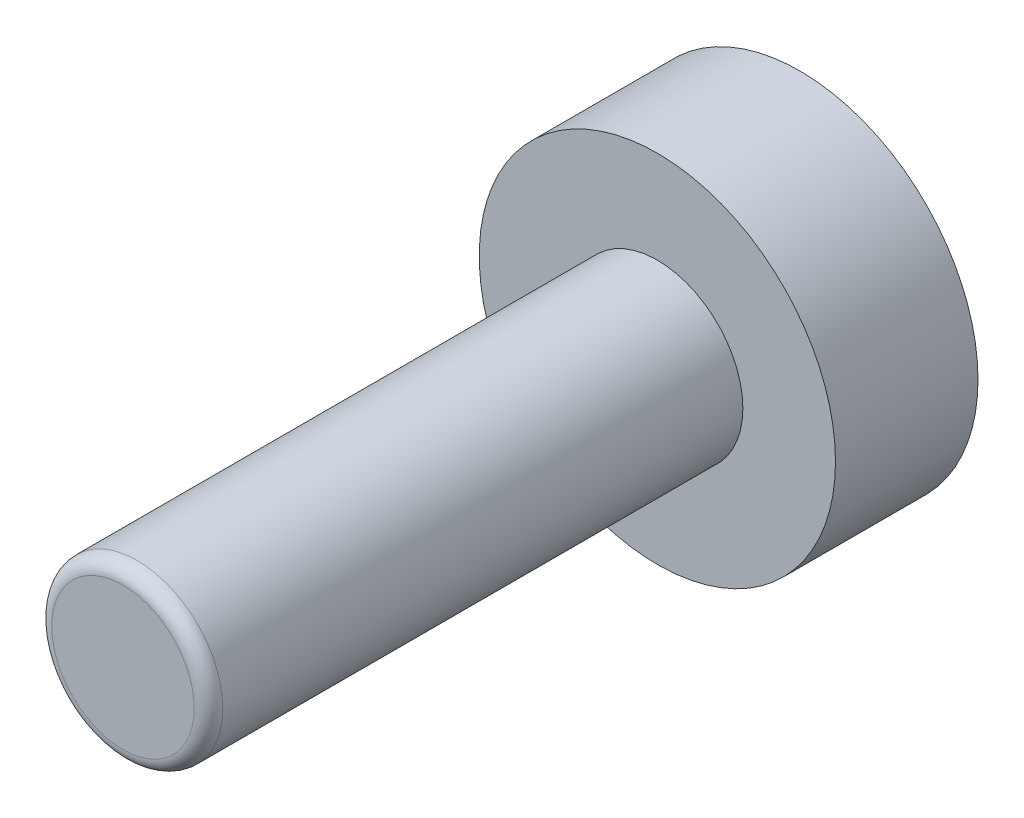
SolidWorks part; units mm, degrees
ref_plane "Plan de face" through (0, 0, 0) normal (0, 0, 1) x (1, 0, 0)
ref_plane "Plan de dessus" through (0, 0, 0) normal (0, 1, 0) x (1, 0, 0)
ref_plane "Plan de droite" through (0, 0, 0) normal (1, 0, 0) x (0, 0, -1)
sketch "Esquisse1" plane through (0, 0, 0) normal (0, 0, 1) x (1, 0, 0)
  circle A0 centre (0, 0) radius 5
  dimension "D1" = 10
extrude "Boss.-Extru.1" add sketch "Esquisse1" along normal blind 4
sketch "Esquisse2" plane through (0, 0, 4) normal (0, 0, 1) x (1, 0, 0)
  circle A0 centre (0, 0) radius 2.4
  dimension "D1" = 4.8
extrude "Boss.-Extru.2" add sketch "Esquisse2" along normal blind 15
fillet "Congé1" radius 0.4 1 edges at (2.4, 0, 19)
